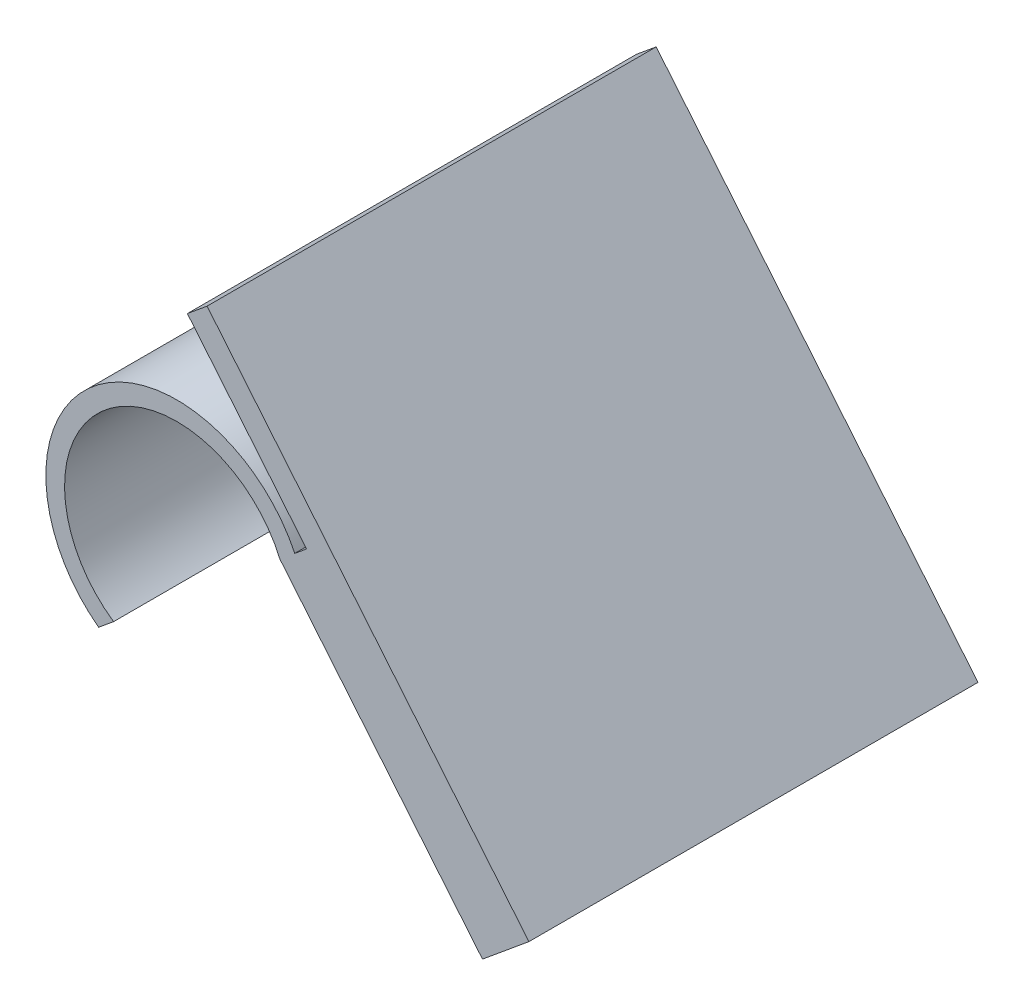
SolidWorks part; units mm, degrees
ref_plane "Front Plane" through (0, 0, 0) normal (0, 0, 1) x (1, 0, 0)
ref_plane "Top Plane" through (0, 0, 0) normal (0, 1, 0) x (1, 0, 0)
ref_plane "Right Plane" through (0, 0, 0) normal (1, 0, 0) x (0, 0, -1)
sketch "Sketch2" plane through (0, 0, 0) normal (0, 0, 1) x (1, 0, 0)
  circle A0 centre (0, 0) radius 38.1
  circle A1 centre (0, 0) radius 44.45
  dimension "D1" = 76.2
  dimension "D2" = 88.9
extrude "Boss-Extrude1" add sketch "Sketch2" along normal blind 152.4
sketch "Sketch3" plane through (0, 0, 152.4) normal (0, 0, 1) x (1, 0, 0)
  line L0 (-26.5316, -35.6634) -> (40.0245, 19.3349)
  line L1 (40.0245, 19.3349) -> (75.8546, -15.6388)
  line L2 (75.8546, -15.6388) -> (-9.8668, -86.4743)
  line L3 (-9.8668, -86.4743) -> (-26.5316, -35.6634)
  circle A0 centre (0, 0) radius 44.45 construction
extrude "Cut-Extrude1" cut sketch "Sketch3" against normal blind 152.4
sketch "Sketch5" plane through (6.7465, -8.1642, 0) normal (0.637, -0.7709, 0) x (-0.7709, -0.637, 0)
  line L1 (-36.5984, -152.4) -> (-57.0338, -152.4)
  line L2 (-36.5984, -152.4) -> (-36.5984, 0)
  line L3 (-36.5984, 0) -> (-57.0338, 0)
  line L4 (-57.0338, -152.4) -> (-57.0338, 0)
extrude "Boss-Extrude2" add sketch "Sketch5" along normal blind 6.35
sketch "Sketch6" plane through (6.7465, -8.1642, 0) normal (-0.637, 0.7709, 0) x (0.7709, 0.637, 0)
  line L0 (57.0338, -152.4) -> (43.1698, -152.4) construction
  line L1 (57.0338, 0) -> (48.3574, 0)
  line L2 (57.0338, 0) -> (57.0338, -152.4)
  line L3 (57.0338, -152.4) -> (48.3574, -152.4)
  line L4 (48.3574, 0) -> (48.3574, -152.4)
extrude "Boss-Extrude3" add sketch "Sketch6" along normal blind 63.5
sketch "Sketch7" plane through (10.7914, -13.0592, 0) normal (0.637, -0.7709, 0) x (0.7709, 0.637, 0)
  line L1 (36.5984, 152.4) -> (57.0338, 152.4)
  line L2 (36.5984, 152.4) -> (36.5984, 0)
  line L3 (36.5984, 0) -> (57.0338, 0)
  line L4 (57.0338, 152.4) -> (57.0338, 0)
extrude "Boss-Extrude4" add sketch "Sketch7" along normal blind 101.6
